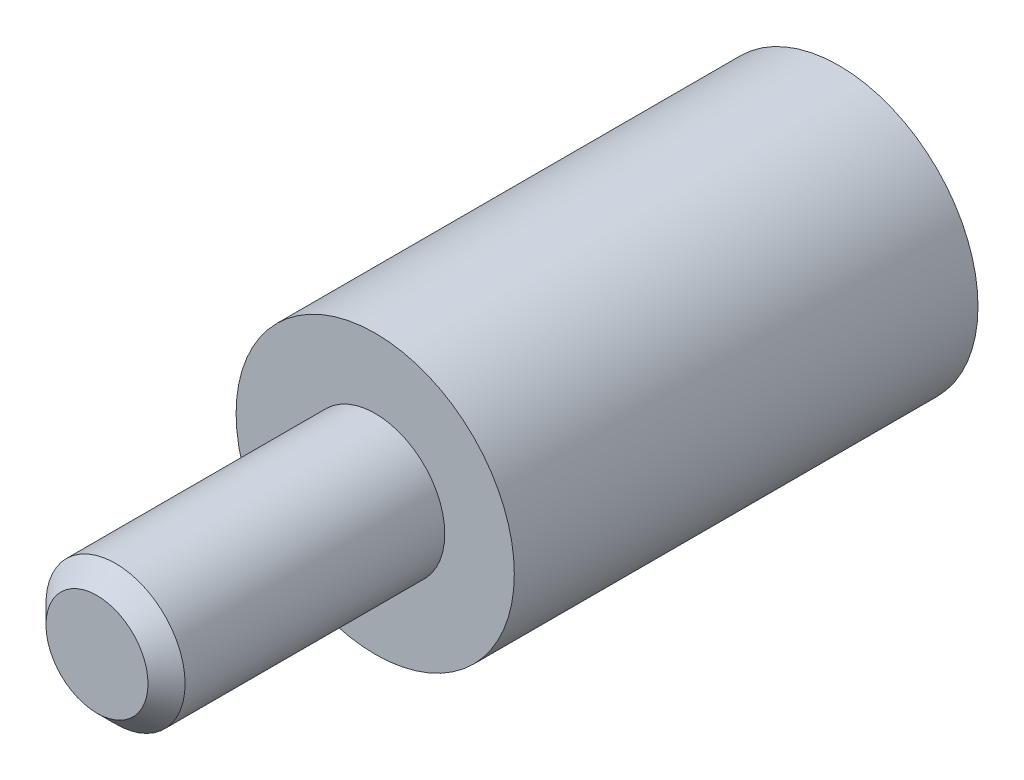
SolidWorks part; units mm, degrees
material "ﾎﾟﾘｵｷｼﾒﾁﾚﾝ(POM)ｱｾﾀｰﾙ共重合体"
ref_plane "正面" through (0, 0, 0) normal (1, 0, 0) x (0, 1, 0)
ref_plane "平面" through (0, 0, 0) normal (0, 0, 1) x (0, 1, 0)
ref_plane "右側面" through (0, 0, 0) normal (0, 1, 0) x (-1, 0, 0)
sketch "ｽｹｯﾁ1" plane through (0, 0, 0) normal (0, 0, 1) x (0, 1, 0)
  circle A0 centre (0, 0) radius 3
  dimension "D1" = 6
extrude "ﾎﾞｽ - 押し出し1" add sketch "ｽｹｯﾁ1" along normal blind 10
sketch "ｽｹｯﾁ2" plane through (0, 0, 10) normal (0, 0, 1) x (1, 0, 0)
  circle A0 centre (0, 0) radius 1.5
  dimension "D1" = 3
extrude "ﾎﾞｽ - 押し出し2" add sketch "ｽｹｯﾁ2" along normal blind 6
sketch "ｽｹｯﾁ3" plane through (0, 0, 0) normal (0, 0, -1) x (1, 0, 0)
  point P0 (0, 0)
hole_wizard "M3x0.5 ねじ穴1" positions "ｽｹｯﾁ3" profile "ｽｹｯﾁ4" tap size "M3x0.5" standard "JIS"
sketch "ｽｹｯﾁ4" plane through (0, 0, 0) normal (1, 0, 0) x (0, 1, 0)
  line L0 (0, 0) -> (0, 9.2511)
  line L1 (0, 9.2511) -> (1.25, 8.5)
  line L2 (1.25, 8.5) -> (1.25, 0)
  line L5 (1.25, 0) -> (0, 0)
  line L10 (0, 9.2511) -> (-1.25, 8.5) construction
  line L11 (0, -6.35) -> (0, 107.95) construction
  dimension "ねじ下穴ﾄﾞﾘﾙ直径" = 2.5
  dimension "ねじ下穴ﾄﾞﾘﾙの深さ" = 8.5
  dimension "ﾄﾞﾘﾙ角度" = 118
cosmetic thread "穴のねじ山1" parameters "D1"=6, "D2"=3
chamfer "面取り1" distance 0.4 angle 45 2 edges at (-1.25, 0, 0) (1.5, 0, 16)
